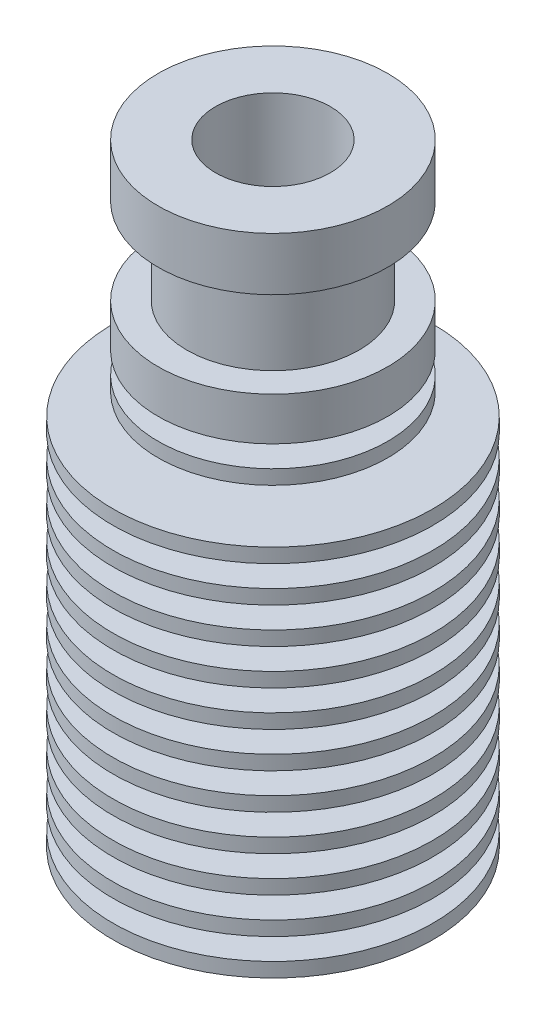
SolidWorks part; units mm, degrees
material "1060 Alloy"
ref_plane "Front Plane" through (0, 0, 0) normal (0, 0, 1) x (1, 0, 0)
ref_plane "Top Plane" through (0, 0, 0) normal (0, 1, 0) x (1, 0, 0)
ref_plane "Right Plane" through (0, 0, 0) normal (1, 0, 0) x (0, 0, -1)
sketch "Sketch1" plane through (0, 0, 0) normal (0, 0, 1) x (1, 0, 0)
  line L0 (3, 0) -> (3, 15.1)
  line L14 (3, 15.1) -> (2.1, 15.7302)
  line L15 (2.1, 15.7302) -> (2.1, 34.8696)
  line L16 (2.1, 34.8696) -> (4, 36.2)
  line L17 (4, 36.2) -> (4, 42.7)
  line L18 (4, 42.7) -> (8, 42.7)
  line L19 (8, 42.7) -> (8, 39)
  line L20 (8, 39) -> (6, 39)
  line L21 (6, 39) -> (6, 33)
  line L22 (6, 33) -> (8, 33)
  line L23 (8, 33) -> (8, 30)
  line L24 (8, 30) -> (5.5, 30)
  line L25 (5.5, 30) -> (8, 0)
  line L26 (8, 0) -> (3, 0)
  line L27 (0, 0) -> (0, 40.6339) construction
  line L28 (0, 0) -> (26.667, 0) construction
  point P18 (8, 40.85)
  dimension "D1" = 6
  dimension "D2" = 12
  dimension "D3" = 16
  dimension "D4" = 8
  dimension "D5" = 4.2
  dimension "D6" = 42.7
  dimension "D7" = 3.7
  dimension "D8" = 3
  dimension "D9" = 6
  dimension "D10" = 6.5
  dimension "D11" = 15.1
  dimension "D12" = 125
  dimension "D13" = 125
  dimension "D14" = 16
  dimension "D15" = 0.5
revolve "Revolve1" add sketch "Sketch1" angle 360 about L27
sketch "Sketch2" plane through (0, 0, 0) normal (0, 0, 1) x (1, 0, 0)
  line L0 (0, 0) -> (0, 67.1932) construction
  line L1 (11.15, 0) -> (3, 0)
  line L2 (11.15, 0) -> (11.15, 1)
  line L3 (11.15, 1) -> (3, 1)
  line L4 (3, 0) -> (3, 1)
  line L5 (-8, 0) -> (8, 0) construction
  dimension "D1" = 22.3
  dimension "D2" = 1
revolve "Revolve2" add sketch "Sketch2" angle 360 about L0
pattern_linear "LPattern1" count 11 spacing 2.5 along (0, 1, 0) of "Revolve2"
sketch "Sketch3" plane through (0, 0, 0) normal (0, 0, 1) x (1, 0, 0)
  line L0 (5.625, 28.5) -> (8, 28.5)
  line L1 (5.8333, 26) -> (5.5, 30) construction
  line L2 (8, 28.5) -> (8, 27.5)
  line L3 (8, 27.5) -> (5.7083, 27.5)
  line L4 (5.7083, 27.5) -> (5.625, 28.5)
  line L6 (-11.15, 25) -> (11.15, 25) construction
  line L7 (8, 30) -> (8, 33) construction
  dimension "D1" = 1
  dimension "D2" = 2.5
revolve "Revolve3" add sketch "Sketch3" angle 360 about axis through (0, 0, 0) along (0, -1, 0)
sketch "Sketch4" plane through (0, 0, 0) normal (0, -1, 0) x (1, 0, 0)
  circle A0 centre (0, 0) radius 3.25
  dimension "D1" = 6.5
extrude "Boss-Extrude1" add sketch "Sketch4" along normal blind 2.1
sketch "Sketch5" plane through (0, -2.1, 0) normal (0, -1, 0) x (1, 0, 0)
  circle A0 centre (0, 0) radius 2.5
  dimension "D1" = 5
extrude "Cut-Extrude1" cut sketch "Sketch5" against normal blind 2.1
